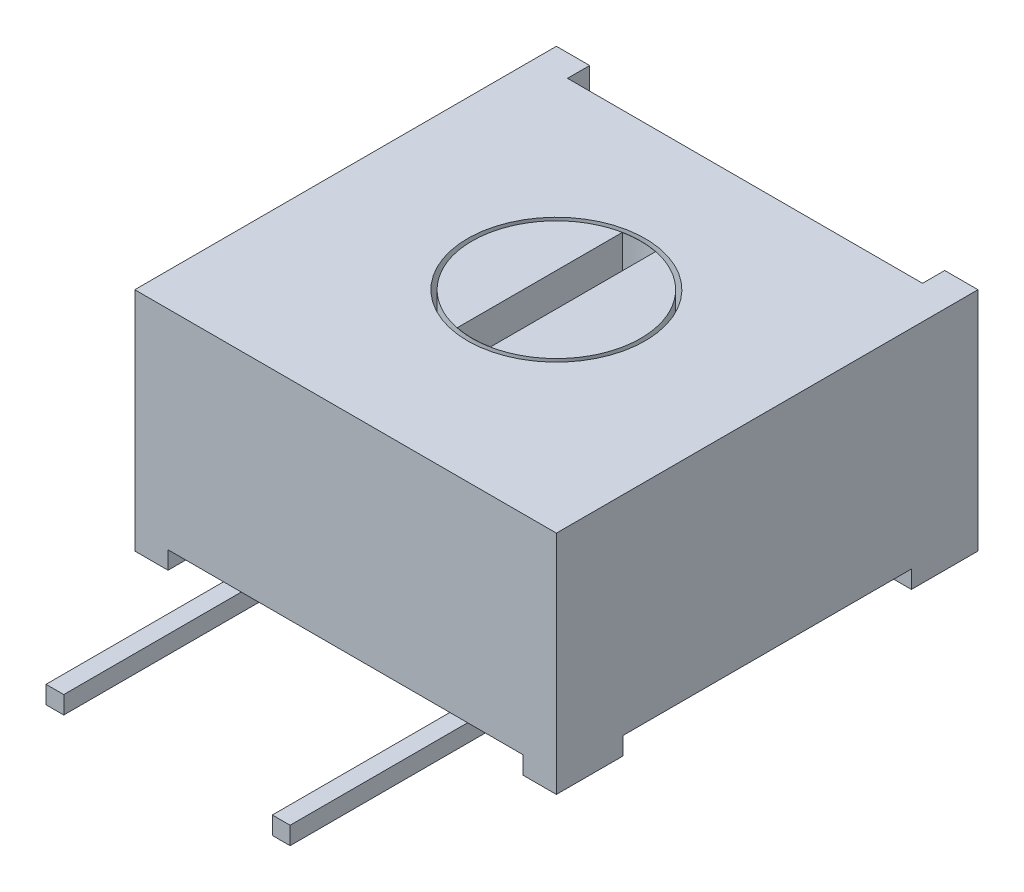
SolidWorks part; units mm, degrees
ref_plane "Front Plane" through (0, 0, 0) normal (0, 0, 1) x (1, 0, 0)
ref_plane "Top Plane" through (0, 0, 0) normal (0, 1, 0) x (1, 0, 0)
ref_plane "Right Plane" through (0, 0, 0) normal (1, 0, 0) x (0, 0, -1)
sketch "Sketch1" plane through (0, 0, 0) normal (0, 1, 0) x (1, 0, 0)
  line L1 (4.75, -4.75) -> (-4.75, -4.75)
  line L2 (4.75, -4.75) -> (4.75, 4.75)
  line L3 (4.75, 4.75) -> (-4.75, 4.75)
  line L4 (-4.75, -4.75) -> (-4.75, 4.75)
  line L5 (4.75, -4.75) -> (-4.75, 4.75) construction
  line L6 (4.75, 4.75) -> (-4.75, -4.75) construction
  point P0 (0, 0)
  dimension "D1" = 9.5
  dimension "D2" = 9.5
extrude "Boss-Extrude1" add sketch "Sketch1" along normal blind 4.7
sketch "Sketch2" plane through (0, 0, 0) normal (0, -1, 0) x (1, 0, 0)
  line L0 (0, 6.8371) -> (0, 0) construction
  line L1 (0, 0) -> (8.3983, 0) construction
  line L2 (4.75, 3.25) -> (4, 3.25)
  line L3 (-4.75, 4.75) -> (-4, 4.75)
  line L4 (-4.75, 4.75) -> (-4.75, 3.25)
  line L5 (-4.75, 3.25) -> (-4, 3.25)
  line L6 (-4, 4.75) -> (-4, 3.25)
  line L7 (4.75, 4.75) -> (4.75, 3.25)
  line L8 (4.75, 4.75) -> (4, 4.75)
  line L9 (4, 4.75) -> (4, 3.25)
  line L10 (4, -4.75) -> (4, -3.25)
  line L11 (4.75, -4.75) -> (4, -4.75)
  line L12 (4.75, -4.75) -> (4.75, -3.25)
  line L13 (-4, -4.75) -> (-4, -3.25)
  line L14 (-4.75, -3.25) -> (-4, -3.25)
  line L15 (-4.75, -4.75) -> (-4.75, -3.25)
  line L16 (-4.75, -4.75) -> (-4, -4.75)
  line L17 (4.75, -3.25) -> (4, -3.25)
  dimension "D1" = 1.5
  dimension "D2" = 0.75
extrude "Boss-Extrude2" add sketch "Sketch2" along normal blind 0.4
sketch "Sketch3" plane through (0, 0, 0) normal (0, -1, 0) x (1, 0, 0)
  line L0 (2.35, 8.75) -> (2.75, 8.75)
  line L1 (-0.2, -2.75) -> (0.2, -2.75)
  line L2 (-0.2, -2.75) -> (-0.2, -8.75)
  line L3 (-0.2, -8.75) -> (0.2, -8.75)
  line L4 (0.2, -2.75) -> (0.2, -8.75)
  line L5 (-0.2, -2.75) -> (0.2, -8.75) construction
  line L6 (-0.2, -8.75) -> (0.2, -2.75) construction
  line L7 (2.35, 8.75) -> (2.35, 2.75)
  line L8 (2.35, 2.75) -> (2.75, 2.75)
  line L9 (2.75, 8.75) -> (2.75, 2.75)
  line L10 (2.35, 8.75) -> (2.75, 2.75) construction
  line L11 (2.35, 2.75) -> (2.75, 8.75) construction
  line L12 (4, -4.75) -> (-4, -4.75) construction
  line L13 (-4, 4.75) -> (4, 4.75) construction
  line L14 (4.75, 3.25) -> (4.75, -3.25) construction
  line L15 (0, 0) -> (0, 9.1806) construction
  line L16 (-2.35, 2.75) -> (-2.75, 8.75) construction
  line L17 (-2.35, 8.75) -> (-2.75, 2.75) construction
  line L18 (-2.75, 8.75) -> (-2.75, 2.75)
  line L19 (-2.35, 2.75) -> (-2.75, 2.75)
  line L20 (-2.35, 8.75) -> (-2.35, 2.75)
  line L21 (-2.35, 8.75) -> (-2.75, 8.75)
  point P0 (0, -5.75)
  point P6 (2.55, 5.75)
  point P23 (-2.55, 5.75)
  dimension "D1" = 2
  dimension "D2" = 2
  dimension "D3" = 2
  dimension "D4" = 0.4
  dimension "D5" = 0.4
  dimension "D6" = 6
  dimension "D7" = 6
extrude "Boss-Extrude3" add sketch "Sketch3" along normal blind 0.4 separate body
sketch "Sketch4" plane through (0, 4.7, 0) normal (0, 1, 0) x (1, 0, 0)
  line L0 (4.75, 4.75) -> (-4.75, 4.75) construction
  line L1 (-4, 4.75) -> (4, 4.75)
  line L2 (-4, 4.75) -> (-4, 4.25)
  line L3 (-4, 4.25) -> (4, 4.25)
  line L4 (4, 4.75) -> (4, 4.25)
  line L5 (4.75, -4.75) -> (4.75, 4.75) construction
  line L6 (-4.75, 4.75) -> (-4.75, -4.75) construction
  dimension "D1" = 0.75
  dimension "D2" = 0.5
  dimension "D3" = 0.75
extrude "Cut-Extrude1" cut sketch "Sketch4" against normal up to surface (4.7 mm away) up to face at (0, 0, -5.75)
sketch "Sketch5" plane through (0, 4.7, 0) normal (0, 1, 0) x (1, 0, 0)
  circle A0 centre (0, 0) radius 2
  dimension "D1" = 4
extrude "Cut-Extrude2" cut sketch "Sketch5" against normal blind 2 and the other way through all
sketch "Sketch6" plane through (0, 2.7, 0) normal (0, 1, 0) x (1, 0, 0)
  circle A2 centre (0, 0) radius 1.9
  circle A3 centre (0, 0) radius 1.9
  dimension "D1" = 0.1
extrude "Boss-Extrude4" add sketch "Sketch6" along normal up to surface (2 mm away) separate body up to face at (0, 4.7, 2)
sketch "Sketch7" plane through (0, 4.7, 0) normal (0, 1, 0) x (1, 0, 0)
  line L2 (0.375, -1.8598) -> (0.375, 1.8598)
  line L4 (-0.375, -1.8598) -> (-0.375, 1.8598)
  line L5 (0.375, -1.8598) -> (-0.375, 1.8598) construction
  line L6 (0.375, 1.8598) -> (-0.375, -1.8598) construction
  arc A0 (-0.375, -1.8598) -> (0.375, -1.8598) centre (0, 0) ccw
  arc A1 (0.375, 1.8598) -> (-0.375, 1.8598) centre (0, 0) ccw
  dimension "D1" = 0.75
extrude "Cut-Extrude3" cut sketch "Sketch7" against normal blind 1
